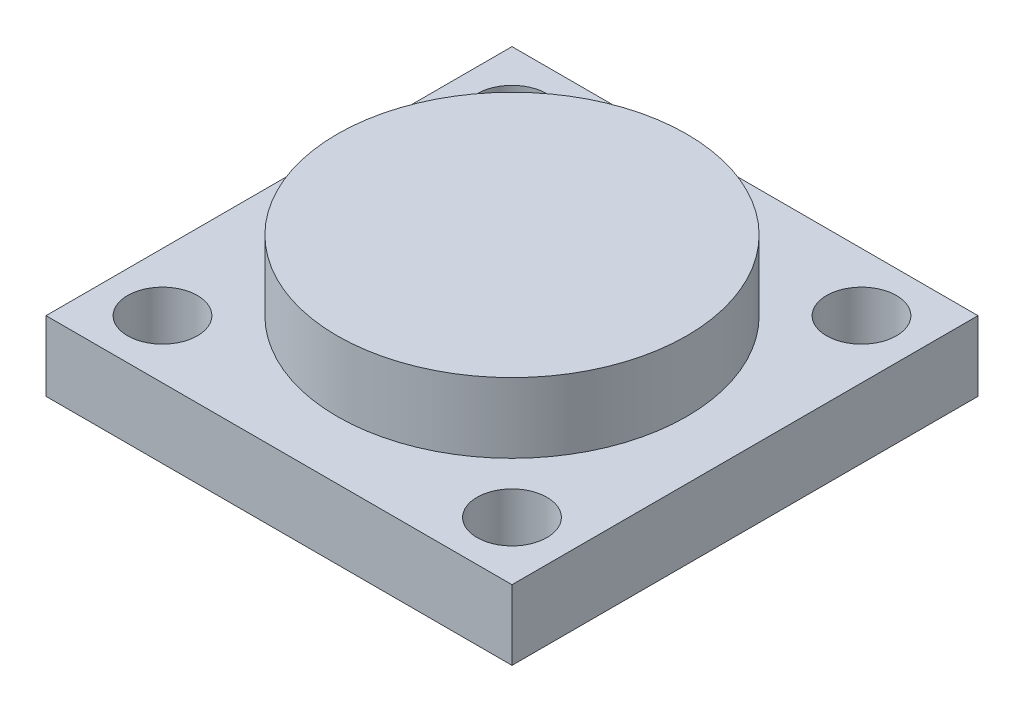
SolidWorks part; units mm, degrees
ref_plane "Front Plane" through (0, 0, 0) normal (0, 0, 1) x (1, 0, 0)
ref_plane "Top Plane" through (0, 0, 0) normal (0, 1, 0) x (1, 0, 0)
ref_plane "Right Plane" through (0, 0, 0) normal (1, 0, 0) x (0, 0, -1)
sketch "Sketch1" plane through (0, 0, 0) normal (0, 1, 0) x (1, 0, 0)
  line L1 (-100, 100) -> (100, 100)
  line L2 (-100, 100) -> (-100, -100)
  line L3 (-100, -100) -> (100, -100)
  line L4 (100, 100) -> (100, -100)
  line L5 (-100, 100) -> (100, -100) construction
  line L6 (-100, -100) -> (100, 100) construction
  dimension "D2" = 200
  dimension "D3" = 200
extrude "Boss-Extrude1" add sketch "Sketch1" along normal blind 30 contours L1 L4 L3 L2
sketch "Sketch3" plane through (0, 30, 0) normal (0, 1, 0) x (1, 0, 0)
  circle A0 centre (0, 0) radius 75
extrude "Boss-Extrude2" add sketch "Sketch3" along normal blind 30
sketch "Sketch4" plane through (0, 30, 0) normal (0, 1, 0) x (1, 0, 0)
  line L0 (-100, 100) -> (100, 100) construction
  line L1 (-100, 100) -> (-100, -100) construction
  line L2 (100, 100) -> (100, -100) construction
  line L3 (-100, -100) -> (100, -100) construction
  circle A0 centre (-75, 75) radius 15
  circle A1 centre (-75, -75) radius 15
  circle A2 centre (75, 75) radius 15
  circle A3 centre (75, -75) radius 15
  dimension "D1" = 25
  dimension "D2" = 25
  dimension "D3" = 25
  dimension "D4" = 25
  dimension "D5" = 25
  dimension "D6" = 25
  dimension "D7" = 25
  dimension "D8" = 25
extrude "Cut-Extrude1" cut sketch "Sketch4" against normal blind 30
